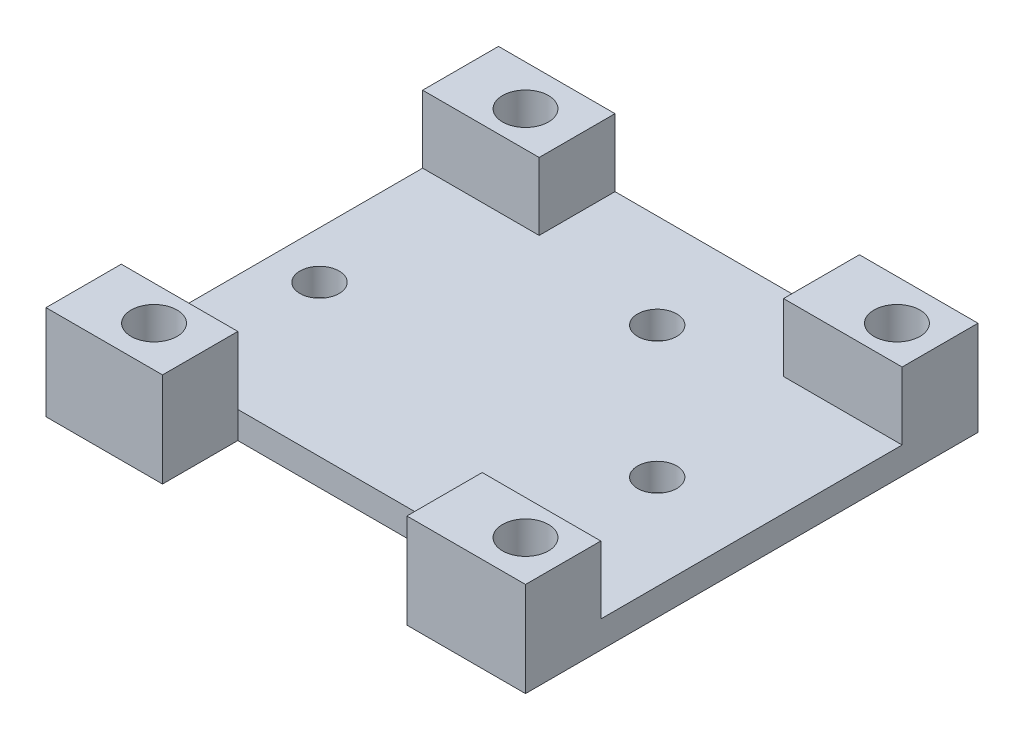
SolidWorks part; units mm, degrees
ref_plane "Front Plane" through (0, 0, 0) normal (0, 0, 1) x (1, 0, 0)
ref_plane "Top Plane" through (0, 0, 0) normal (0, 1, 0) x (1, 0, 0)
ref_plane "Right Plane" through (0, 0, 0) normal (1, 0, 0) x (0, 0, -1)
sketch "Sketch1" plane through (0, 0, 0) normal (0, 1, 0) x (1, 0, 0)
  line L1 (-20, 16.75) -> (20, 16.75)
  line L2 (-20, 16.75) -> (-20, -16.75)
  line L3 (-20, -16.75) -> (20, -16.75)
  line L4 (20, 16.75) -> (20, -16.75)
  line L5 (-20, 16.75) -> (20, -16.75) construction
  line L6 (-20, -16.75) -> (20, 16.75) construction
  point P0 (0, 0)
  dimension "D1" = 40
  dimension "D2" = 33.5
extrude "Boss-Extrude1" add sketch "Sketch1" along normal blind 7
hole_wizard "M3 Clearance Hole1" positions "3DSketch1" profile "Sketch2" hole size "M3" standard "ANSI Metric" end condition through all
sketch3d "3DSketch1"
  line L0 (-20, 7, -16.75) -> (-20, 7, 16.75) construction
  line L1 (-20, 7, 16.75) -> (20, 7, 16.75) construction
  line L2 (20, 7, -16.75) -> (-20, 7, -16.75) construction
  line L3 (20, 7, 16.75) -> (20, 7, -16.75) construction
  point P0 (-10.5, 7, 13.75)
  point P2 (17, 7, -13.75)
  dimension "D1" = 9.5
  dimension "D2" = 3
  dimension "D3" = 3
  dimension "D4" = 3
  dimension "D5" = 38.8909
sketch "Sketch2" plane through (-10.5, 7, 13.75) normal (1, 0, 0) x (0, 0, 1)
  line L0 (0, 0) -> (0, 7)
  line L1 (0, 7) -> (1.7, 7)
  line L2 (1.7, 7) -> (1.7, 0)
  line L5 (1.7, 0) -> (0, 0)
  line L11 (0, -6.35) -> (0, 107.95) construction
  dimension "Thru Hole Dia." = 3.4
  dimension "Thru Hole Depth" = 7
sketch "Sketch3" plane through (0, 7, 0) normal (0, 1, 0) x (1, 0, 0)
  line L0 (-20, -11.1763) -> (20, -11.1763)
  line L1 (-20, 16.75) -> (11.2193, 16.75)
  line L2 (-20, 16.75) -> (-20, -11.1763)
  line L4 (11.2193, 16.75) -> (11.2193, -11.1763)
  line L6 (-6.8726, -11.1763) -> (-6.8726, -16.75)
  line L7 (-6.8726, -16.75) -> (20, -16.75)
  line L8 (20, -11.1763) -> (20, -16.75)
  line L9 (11.2193, 11.1333) -> (20, 11.1333)
  line L12 (20, 11.1333) -> (20, -11.1763)
sketch "Sketch4" plane through (0, 7, 0) normal (0, 1, 0) x (1, 0, 0)
  line L1 (-20, 16.75) -> (11.2193, 16.75)
  line L2 (-20, 16.75) -> (-20, -11.1763)
  line L3 (-20, -11.1763) -> (11.2193, -11.1763)
  line L4 (11.2193, 16.75) -> (11.2193, -11.1763)
extrude "Cut-Extrude1" cut sketch "Sketch4" against normal blind 5
sketch "Sketch5" plane through (0, 7, 0) normal (0, 1, 0) x (1, 0, 0)
  line L1 (11.2193, 11.1333) -> (20, 11.1333)
  line L2 (11.2193, 11.1333) -> (11.2193, -11.1763)
  line L3 (11.2193, -11.1763) -> (20, -11.1763)
  line L4 (20, 11.1333) -> (20, -11.1763)
extrude "Cut-Extrude2" cut sketch "Sketch5" against normal blind 5
hole_wizard "M2.5 Clearance Hole2" positions "3DSketch3" profile "Sketch8" hole size "M2.5" standard "ANSI Metric" end condition through all
sketch3d "3DSketch3"
  line L5 (-20, 2, -16.75) -> (-20, 2, 11.1763) construction
  line L8 (11.2193, 2, -16.75) -> (-20, 2, -16.75) construction
  line L9 (20, 2, 11.1763) -> (20, 2, -11.1333) construction
  point P0 (-12, 2, 0)
  point P2 (13, 2, 0)
  point P4 (3.25, 2, -9.75)
  dimension "D1" = 8
  dimension "D7" = 25
  dimension "D2" = 16.75
  dimension "D8" = 32
  dimension "D3" = 7
  dimension "D4" = 7
  dimension "D5" = 16.75
  dimension "D6" = 16.75
sketch "Sketch8" plane through (-12, 2, 0) normal (1, 0, 0) x (0, 0, 1)
  line L0 (0, 0) -> (0, 2)
  line L1 (0, 2) -> (1.45, 2)
  line L2 (1.45, 2) -> (1.45, 0)
  line L5 (1.45, 0) -> (0, 0)
  line L11 (0, -6.35) -> (0, 107.95) construction
  dimension "Thru Hole Dia." = 2.9
  dimension "Thru Hole Depth" = 2
sketch "Sketch12" plane through (0, 7, 0) normal (0, 1, 0) x (1, 0, 0)
  line L1 (-6.8726, -11.1763) -> (20, -11.1763)
  line L2 (-6.8726, -11.1763) -> (-6.8726, -16.75)
  line L3 (-6.8726, -16.75) -> (20, -16.75)
  line L4 (20, -11.1763) -> (20, -16.75)
extrude "Cut-Extrude4" cut sketch "Sketch12" against normal through all
sketch "Sketch13" plane through (0, 0, 0) normal (0, -1, 0) x (1, 0, 0)
  line L1 (11.2193, 11.1763) -> (20, 11.1763)
  line L2 (11.2193, 11.1763) -> (11.2193, 16.75)
  line L3 (11.2193, 16.75) -> (20, 16.75)
  line L4 (20, 11.1763) -> (20, 16.75)
extrude "Boss-Extrude2" add sketch "Sketch13" against normal up to vertex (7 mm away)
sketch "Sketch14" plane through (0, 2, 0) normal (0, 1, 0) x (1, 0, 0)
  line L0 (-20, 16.75) -> (11.2193, 16.75) construction
  line L1 (-6.8726, 16.75) -> (-20, 16.75)
  line L2 (-6.8726, 16.75) -> (-6.8726, 11.1333)
  line L3 (-6.8726, 11.1333) -> (-20, 11.1333)
  line L4 (-20, 16.75) -> (-20, 11.1333)
  line L6 (11.2193, 11.1333) -> (20, 11.1333) construction
  line L7 (-20, 16.75) -> (-20, -11.1763) construction
  dimension "D1" = 0
  dimension "D2" = 5.6167
  dimension "D3" = 0
extrude "Boss-Extrude3" add sketch "Sketch14" along normal up to vertex (5 mm away)
hole_wizard "M3 Clearance Hole2" positions "Sketch16" profile "Sketch15" hole size "M3" standard "ANSI Metric" end condition through all
sketch "Sketch16" plane through (0, 7, 0) normal (0, 1, 0) x (1, 0, 0)
  line L0 (-20, 16.75) -> (-20, -11.1763) construction
  line L1 (-20, 16.75) -> (11.2193, 16.75) construction
  line L2 (20, -11.1763) -> (20, -16.75) construction
  line L3 (-6.8726, -16.75) -> (20, -16.75) construction
  point P0 (-10.5, 13.75)
  point P2 (17, -13.75)
  dimension "D1" = 9.5
  dimension "D2" = 3
  dimension "D3" = 3
  dimension "D4" = 3
  dimension "D5" = 38.8909
sketch "Sketch15" plane through (-10.5, 7, -13.75) normal (1, 0, 0) x (0, 0, 1)
  line L0 (0, 0) -> (0, 7)
  line L1 (0, 7) -> (1.7, 7)
  line L2 (1.7, 7) -> (1.7, 0)
  line L5 (1.7, 0) -> (0, 0)
  line L11 (0, -6.35) -> (0, 107.95) construction
  dimension "Thru Hole Dia." = 3.4
  dimension "Thru Hole Depth" = 7
sketch "Sketch17" plane through (0, 7, 0) normal (0, 1, 0) x (1, 0, 0)
  line L0 (-20, -16.75) -> (-6.8726, -16.75) construction
  line L1 (-20, 16.75) -> (-15.5, 16.75)
  line L2 (-20, 16.75) -> (-20, -16.75)
  line L3 (-20, -16.75) -> (-15.5, -16.75)
  line L4 (-15.5, 16.75) -> (-15.5, -16.75)
  dimension "D1" = 4.5
extrude "Cut-Extrude5" cut sketch "Sketch17" against normal through all
